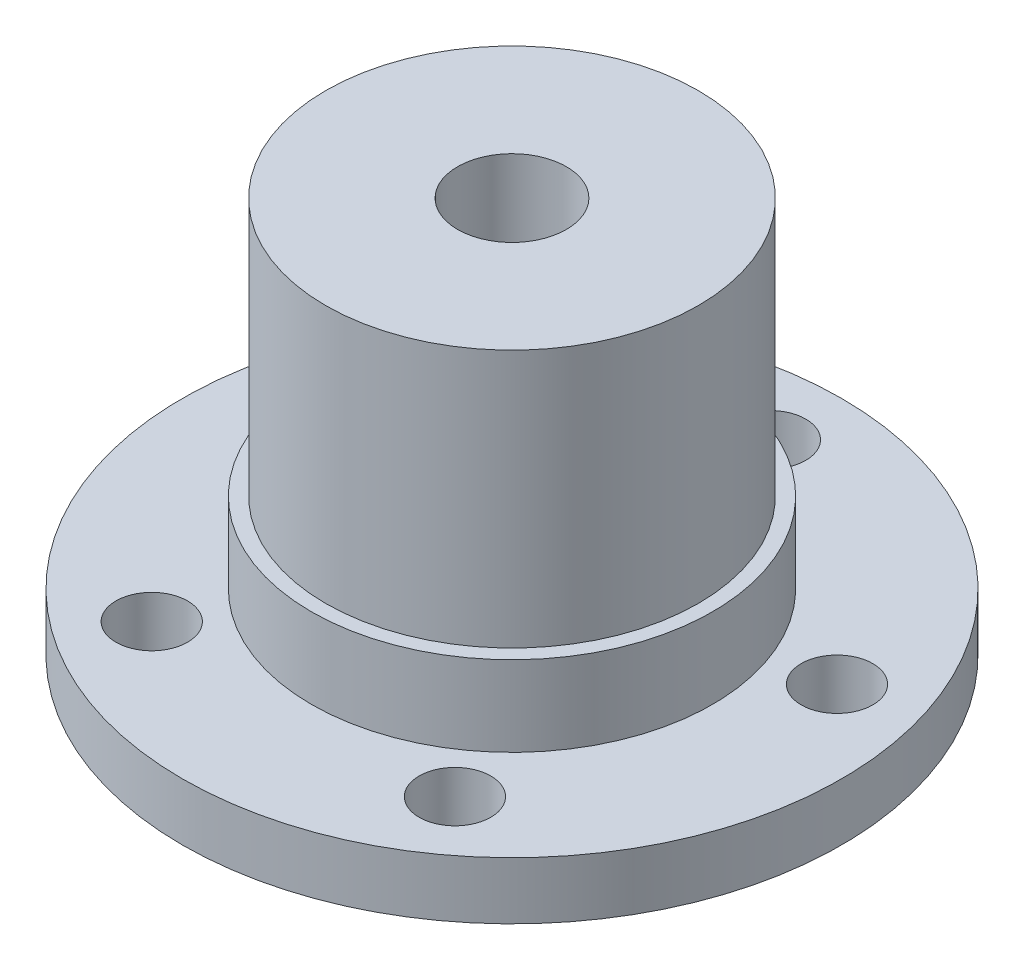
SolidWorks part; units mm, degrees
material "6061-T6 (SS)"
ref_plane "Front Plane" through (0, 0, 0) normal (0, 0, 1) x (1, 0, 0)
ref_plane "Top Plane" through (0, 0, 0) normal (0, 1, 0) x (1, 0, 0)
ref_plane "Right Plane" through (0, 0, 0) normal (1, 0, 0) x (0, 0, -1)
sketch "Sketch1" plane through (0, 0, 0) normal (0, 0, 1) x (1, 0, 0)
  line L0 (0, 0) -> (0, 13.8025) construction
  line L1 (0, 13.8025) -> (6.5, 13.8025)
  line L2 (6.5, 13.8025) -> (6.5, 4.8)
  line L3 (7, 2) -> (11.5, 2)
  line L4 (11.5, 2) -> (11.5, 0)
  line L5 (11.5, 0) -> (0, 0)
  line L6 (0, 0) -> (0, 13.8025)
  line L7 (6.5, 4.8) -> (7, 4.8)
  line L8 (7, 4.8) -> (7, 2)
  dimension "D1" = 13.8025
  dimension "D2" = 6.5
  dimension "D3" = 2
  dimension "D4" = 23
  dimension "D5" = 0.5
  dimension "D6" = 2.8
revolve "Revolve1" add sketch "Sketch1" angle 360 about L0
hole_wizard "M3x0.5 Tapped Hole1" positions "Sketch3" profile "Sketch4" tap size "M3x0.5" standard "ANSI Metric" end condition through all
sketch "Sketch3" plane through (0, 0, 0) normal (0, -1, 0) x (-1, 0, 0)
  point P0 (0, 9)
  point P35 (8.5595, 2.7812)
  point P36 (5.2901, -7.2812)
  point P37 (-5.2901, -7.2812)
  point P38 (-8.5595, 2.7812)
  point P39 (0, 0)
  dimension "D1" = 9
  dimension "D2" = 5
sketch "Sketch4" plane through (0, 0, -9) normal (1, 0, 0) x (0, 0, -1)
  line L0 (0, 0) -> (0, 13.8025)
  line L1 (0, 13.8025) -> (1.25, 13.8025)
  line L2 (1.25, 13.8025) -> (1.25, 0)
  line L5 (1.25, 0) -> (0, 0)
  line L11 (0, -6.35) -> (0, 29.3541) construction
  dimension "Thru Tap Drill Dia." = 2.5
  dimension "Thru Tap Drill Depth" = 13.8025
cosmetic thread "Hole Thread1"
cosmetic thread "Hole Thread2"
cosmetic thread "Hole Thread3"
cosmetic thread "Hole Thread4"
cosmetic thread "Hole Thread5"
cosmetic thread "Hole Thread6"
hole_wizard "#10-24 Tapped Hole1" positions "Sketch9" profile "Sketch8" tap size "#10-24" standard "ANSI Inch"
sketch "Sketch9" plane through (0, 13.8025, 0) normal (0, 1, 0) x (1, 0, 0)
  point P0 (0, 0)
sketch "Sketch8" plane through (0, 13.8025, 0) normal (1, 0, 0) x (0, 0, 1)
  line L0 (0, 0) -> (0, 13.8408)
  line L1 (0, 13.8408) -> (1.8986, 12.7)
  line L2 (1.8986, 12.7) -> (1.8986, 0)
  line L5 (1.8986, 0) -> (0, 0)
  line L10 (0, 13.8408) -> (-1.8987, 12.7) construction
  line L11 (0, -6.35) -> (0, 107.95) construction
  dimension "Tap Drill Dia." = 3.7973
  dimension "Tap Drill Depth" = 12.7
  dimension "Drill Angle" = 118
cosmetic thread "Hole Thread8" parameters "D1"=9.65, "D2"=4.826
